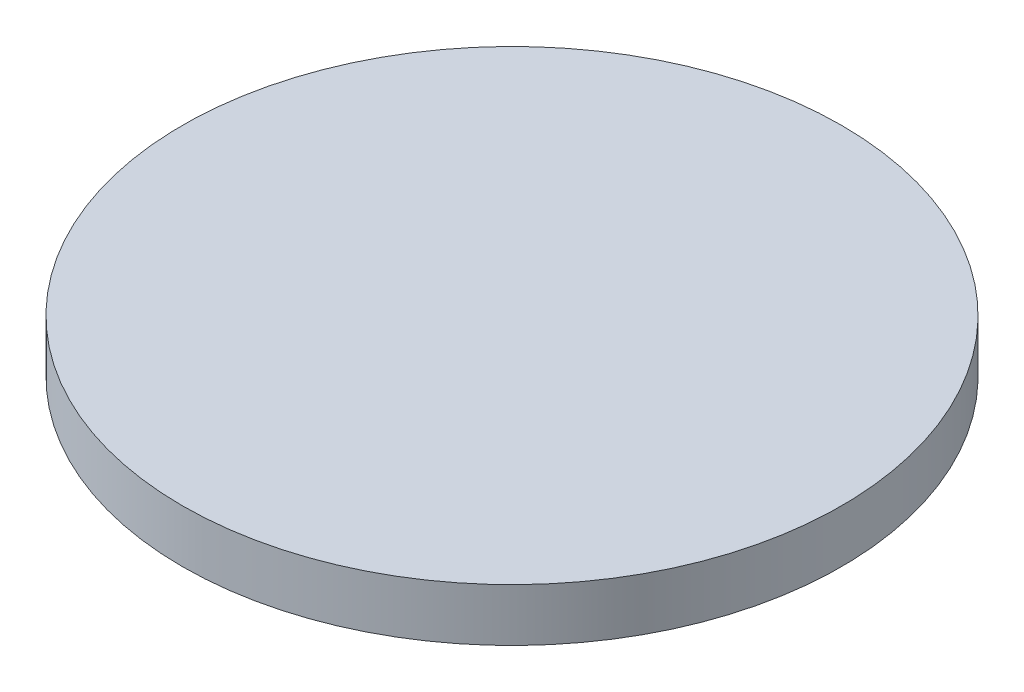
SolidWorks part; units mm, degrees
ref_plane "Front Plane" through (0, 0, 0) normal (0, 0, 1) x (1, 0, 0)
ref_plane "Top Plane" through (0, 0, 0) normal (0, 1, 0) x (1, 0, 0)
ref_plane "Right Plane" through (0, 0, 0) normal (1, 0, 0) x (0, 0, -1)
sketch "Sketch1" plane through (0, 0, 0) normal (0, 1, 0) x (1, 0, 0)
  circle A0 centre (0, 0) radius 25
  dimension "D1" = 50
extrude "Boss-Extrude1" add sketch "Sketch1" along normal blind 4
